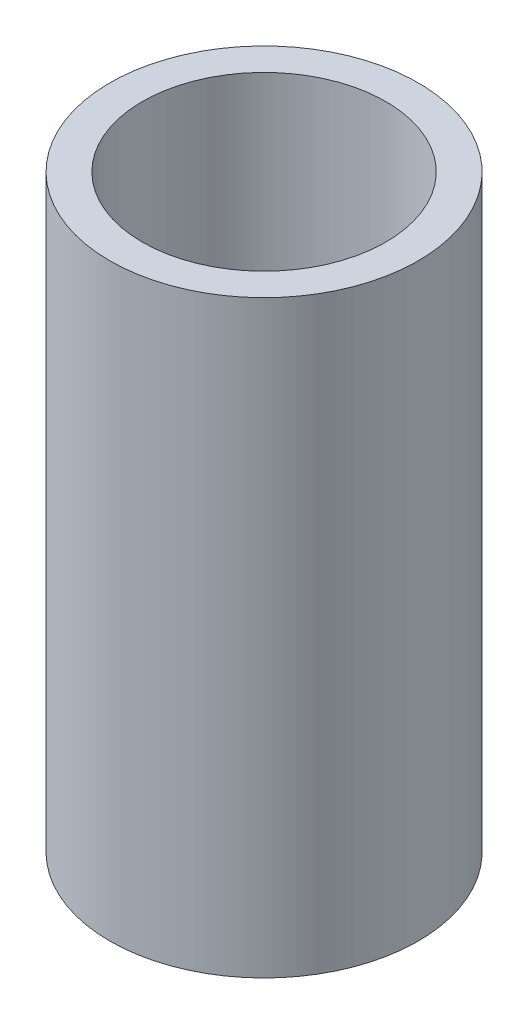
SolidWorks part; units mm, degrees
material "5052-O"
ref_plane "正面" through (0, 0, 0) normal (0, 0, 1) x (1, 0, 0)
ref_plane "平面" through (0, 0, 0) normal (0, 1, 0) x (1, 0, 0)
ref_plane "右側面" through (0, 0, 0) normal (1, 0, 0) x (0, 0, -1)
sketch "ｽｹｯﾁ1" plane through (0, 0, 0) normal (0, 1, 0) x (1, 0, 0)
  circle A0 centre (0, 0) radius 3.925
  circle A1 centre (0, 0) radius 3.1
extrude "ﾎﾞｽ - 押し出し1" add sketch "ｽｹｯﾁ1" along normal blind 15
